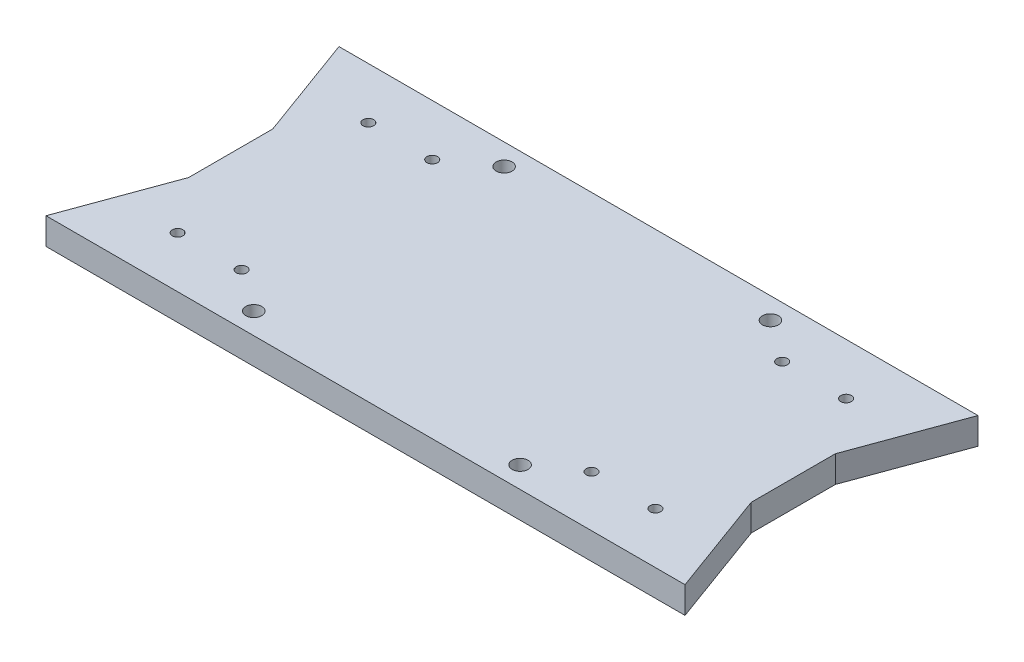
SolidWorks part; units mm, degrees
material "ABS PC"
ref_plane "Front Plane" through (0, 0, 0) normal (0, 0, 1) x (1, 0, 0)
ref_plane "Top Plane" through (0, 0, 0) normal (0, 1, 0) x (1, 0, 0)
ref_plane "Right Plane" through (0, 0, 0) normal (1, 0, 0) x (0, 0, -1)
sketch "Sketch1" plane through (0, 0, 0) normal (0, 1, 0) x (1, 0, 0)
  line L0 (28.7276, 102.6327) -> (-38.3337, 102.6327) construction
  line L1 (-38.3337, 32.7827) -> (28.7276, 32.7827)
  line L2 (-38.3337, 32.7827) -> (-38.3337, 102.6327)
  line L3 (-38.3337, 102.6327) -> (28.7276, 102.6327)
  line L4 (28.7276, 32.7827) -> (28.7276, 102.6327)
  line L5 (-38.3337, 32.7827) -> (28.7276, 32.7827) construction
  line L6 (-38.3337, 102.6327) -> (-38.3337, 32.7827) construction
  circle A1 centre (3.3813, 90.4077) radius 1.27
  circle A2 centre (18.6213, 90.4077) radius 1.27
  circle A3 centre (3.3813, 44.9477) radius 1.27
  circle A4 centre (18.6213, 44.9477) radius 1.27
  dimension "D5" = 2.54
  dimension "D6" = 2.54
  dimension "D7" = 2.54
  dimension "D8" = 2.54
  dimension "D1" = 0
  dimension "D2" = 0
  dimension "D3" = 0
  dimension "D4" = 0
extrude "Boss-Extrude1" add sketch "Sketch1" along normal blind 6.35
sketch "Sketch2" plane through (0, 6.35, 0) normal (0, 1, 0) x (1, 0, 0)
  line L1 (28.7276, 57.6777) -> (7.7513, 57.6777)
  line L2 (28.7276, 57.6777) -> (28.7276, 77.7377)
  line L3 (28.7276, 77.7377) -> (7.7513, 77.7377)
  line L4 (7.7513, 57.6777) -> (7.7513, 77.7377)
extrude "Boss-Extrude2" add sketch "Sketch2" along normal blind 12.7
sketch "Sketch3" plane through (0, 6.35, 0) normal (0, 1, 0) x (1, 0, 0)
  line L1 (37.8413, 102.6327) -> (28.7276, 77.7377)
  line L2 (28.7276, 77.7377) -> (28.7276, 102.6327)
  line L3 (28.7276, 102.6327) -> (37.8413, 102.6327)
  line L4 (28.7276, 57.6777) -> (37.8413, 32.7827)
  line L5 (37.8413, 32.7827) -> (28.7276, 32.7827)
  line L6 (28.7276, 32.7827) -> (28.7276, 57.6777)
extrude "Boss-Extrude3" add sketch "Sketch3" against normal blind 6.35
mirror "Mirror2" about plane through (-38.3337, 6.35, -32.7827) normal (1, 0, 0) of "Boss-Extrude1", "Boss-Extrude2", "Boss-Extrude3"
sketch "Sketch4" plane through (0, 0, -32.7827) normal (0, 0, 1) x (1, 0, 0)
  line L1 (37.8413, 6.35) -> (-133.1569, 6.35)
  line L2 (37.8413, 6.35) -> (37.8413, 24.3471)
  line L3 (37.8413, 24.3471) -> (-133.1569, 24.3471)
  line L4 (-133.1569, 6.35) -> (-133.1569, 24.3471)
extrude "Cut-Extrude1" cut sketch "Sketch4" against normal through all
sketch "Sketch5" plane through (0, 0, 0) normal (0, -1, 0) x (1, 0, 0)
  circle A1 centre (21.0248, -94.445) radius 0.1639
sketch "Sketch6" plane through (0, 0, 0) normal (0, -1, 0) x (-1, 0, 0)
  circle A0 centre (-37.8413, 67.7077) radius 31.75
  dimension "D1" = 63.5
sketch "Sketch7" plane through (0, 6.35, 0) normal (0, 1, 0) x (1, 0, 0)
  circle A0 centre (3.3813, 90.4077) radius 1.2687
  circle A1 centre (18.6213, 90.4077) radius 1.2687
  circle A2 centre (3.3813, 44.9477) radius 1.2687
  circle A4 centre (18.6213, 44.9477) radius 1.2687
  dimension "D1" = 2.5375
  dimension "D2" = 2.5375
  dimension "D3" = 2.5375
  dimension "D4" = 2.5375
sketch "Sketch8" plane through (0, 6.35, 0) normal (0, 1, 0) x (1, 0, 0)
  circle A4 centre (-6.5587, 97.5527) radius 1.905
  circle A5 centre (-6.5587, 37.8627) radius 1.905
  circle A6 centre (-6.5587, 37.8627) radius 1.2446 construction
  circle A7 centre (-171.9188, 187.896) radius 1.905
  circle A8 centre (-70.0587, 97.5527) radius 1.905
  circle A9 centre (-70.0587, 37.8627) radius 1.905
  circle A10 centre (-70.0587, 37.8627) radius 1.2446 construction
  circle A11 centre (-70.0587, 97.5527) radius 1.2446 construction
  circle A12 centre (-6.5587, 97.5527) radius 1.2446 construction
  dimension "D1" = 3.81
extrude "Cut-Extrude3" cut sketch "Sketch8" against normal blind 13.716
